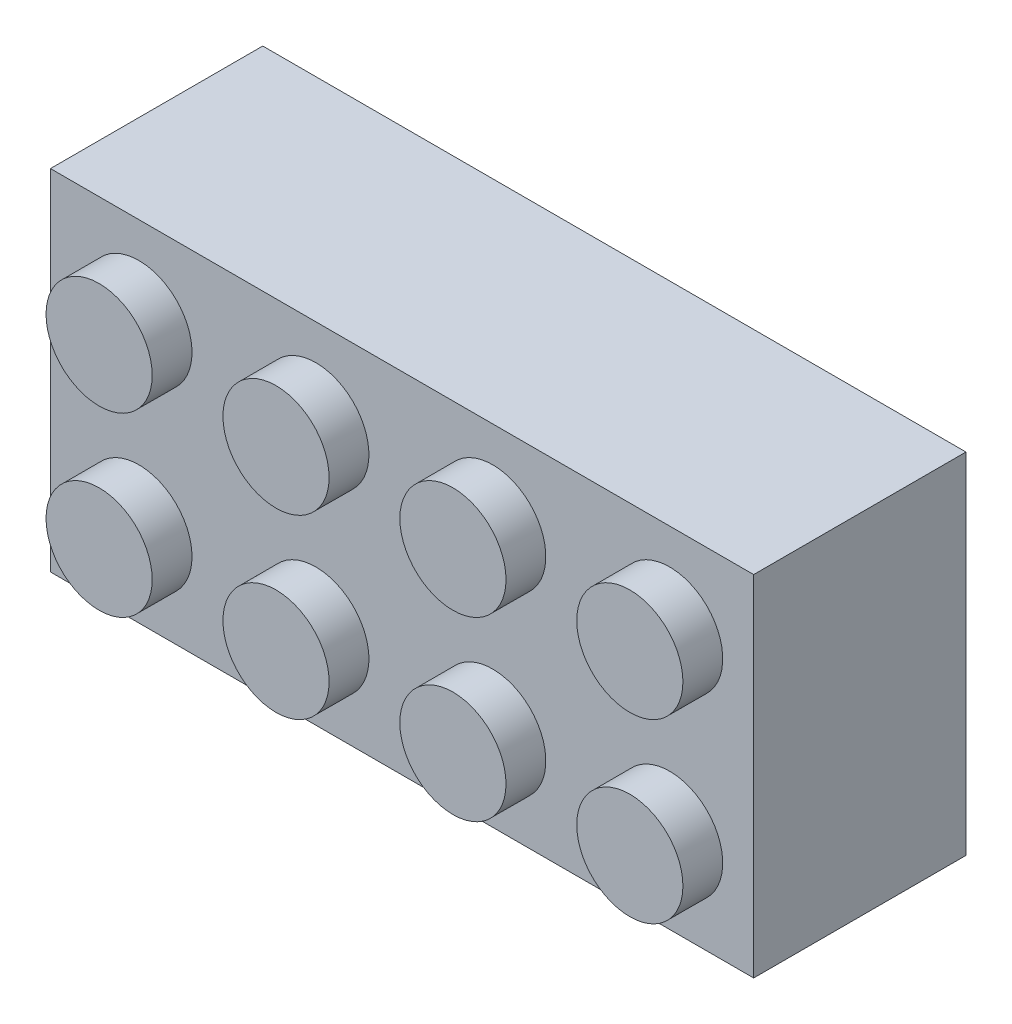
SolidWorks part; units mm, degrees
material "ABS"
ref_plane "Front Plane" through (0, 0, 0) normal (0, 0, 1) x (1, 0, 0)
ref_plane "Top Plane" through (0, 0, 0) normal (0, 1, 0) x (1, 0, 0)
ref_plane "Right Plane" through (0, 0, 0) normal (1, 0, 0) x (0, 0, -1)
sketch "Sketch1" plane through (0, 0, 0) normal (0, 0, 1) x (1, 0, 0)
  line L1 (-15.9, -7.9) -> (15.9, -7.9)
  line L2 (-15.9, -7.9) -> (-15.9, 7.9)
  line L3 (-15.9, 7.9) -> (15.9, 7.9)
  line L4 (15.9, -7.9) -> (15.9, 7.9)
  line L5 (-15.9, -7.9) -> (15.9, 7.9) construction
  line L6 (-15.9, 7.9) -> (15.9, -7.9) construction
  point P0 (0, 0)
  dimension "D1" = 31.8
  dimension "D2" = 15.8
extrude "Boss-Extrude1" add sketch "Sketch1" along normal blind 9.6
ref_plane "Plane1" through (0, 0, 9.6) normal (0, 0, 1) x (1, 0, 0)
sketch "Sketch2" plane through (0, 0, 9.6) normal (0, 0, 1) x (1, 0, 0)
  line L0 (-15.9, 7.9) -> (-15.9, -7.9) construction
  line L1 (15.9, 7.9) -> (-15.9, 7.9) construction
  circle A0 centre (-11.9, 3.9) radius 2.4
  circle A1 centre (-3.9, 3.9) radius 2.4
  circle A2 centre (4.1, 3.9) radius 2.4
  circle A3 centre (12.1, 3.9) radius 2.4
  circle A4 centre (-3.9, -4.1) radius 2.4
  circle A5 centre (4.1, -4.1) radius 2.4
  circle A6 centre (12.1, -4.1) radius 2.4
  circle A7 centre (-11.9, -4.1) radius 2.4
  dimension "D1" = 4.8
  dimension "D2" = 4
  dimension "D3" = 4
  dimension "D4" = 4
  dimension "D5" = 2
extrude "Boss-Extrude2" add sketch "Sketch2" along normal blind 1.8
sketch "Sketch3" plane through (0, 0, 9.6) normal (0, 0, 1) x (1, 0, 0)
  line L0 (-15.9, 7.9) -> (-15.9, -7.9) construction
  circle A0 centre (-11.9, 3.9) radius 1.3
  circle A2 centre (-3.9, 3.9) radius 1.3
  circle A3 centre (4.1, 3.9) radius 1.3
  circle A4 centre (12.1, 3.9) radius 1.3
  circle A5 centre (-3.9, -4.1) radius 1.3
  circle A6 centre (4.1, -4.1) radius 1.3
  circle A7 centre (12.1, -4.1) radius 1.3
  circle A8 centre (-11.9, -4.1) radius 1.3
  dimension "D1" = 2.6
  dimension "D2" = 4
  dimension "D3" = 4
  dimension "D4" = 2
extrude "Cut-Extrude1" cut sketch "Sketch3" against normal blind 20.7 from offset 0.7
sketch "Sketch4" plane through (0, 0, 0) normal (0, 0, 1) x (1, 0, 0)
  line L0 (0, 20.8206) -> (0, -20.114) construction
  line L1 (-15.9, 7.9) -> (-15.9, -7.9) construction
  line L2 (0, 0) -> (-22.9786, 0) construction
  line L3 (-14.7, 3.4) -> (-14.7, -3.4)
  line L4 (-14.7, -3.4) -> (-14.5, -3.4)
  line L5 (-14.5, -3.4) -> (-14.5, -4.6)
  line L6 (-14.5, -4.6) -> (-14.7, -4.6)
  line L7 (-14.7, -4.6) -> (-14.7, -6.7)
  line L8 (-14.7, -6.7) -> (-12.6, -6.7)
  line L9 (-12.6, -6.7) -> (-12.6, -6.5)
  line L10 (-12.6, -6.5) -> (-11.4, -6.5)
  line L11 (-11.4, -6.5) -> (-11.4, -6.7)
  line L12 (-11.4, -6.7) -> (-4.6, -6.7)
  line L13 (-4.6, -6.7) -> (-4.6, -6.5)
  line L14 (-4.6, -6.5) -> (-3.4, -6.5)
  line L15 (-3.4, -6.5) -> (-3.4, -6.7)
  line L16 (-3.4, -6.7) -> (-0.55, -6.7)
  line L17 (-15.9, -7.9) -> (15.9, -7.9) construction
  line L18 (-0.55, -6.7) -> (-0.55, -3.2031)
  line L19 (-3.25, 0) -> (-4.75, 0)
  line L20 (-11.25, 0) -> (-14.7, 0)
  line L21 (-0.55, 6.7) -> (-0.55, 3.2031)
  line L22 (-3.4, 6.7) -> (-0.55, 6.7)
  line L23 (-3.4, 6.5) -> (-3.4, 6.7)
  line L24 (-4.6, 6.5) -> (-3.4, 6.5)
  line L25 (-4.6, 6.7) -> (-4.6, 6.5)
  line L26 (-11.4, 6.7) -> (-4.6, 6.7)
  line L27 (-11.4, 6.5) -> (-11.4, 6.7)
  line L28 (-12.6, 6.5) -> (-11.4, 6.5)
  line L29 (-12.6, 6.7) -> (-12.6, 6.5)
  line L30 (-14.7, 6.7) -> (-12.6, 6.7)
  line L31 (-14.7, 4.6) -> (-14.7, 6.7)
  line L32 (-14.5, 4.6) -> (-14.7, 4.6)
  line L33 (-14.5, 3.4) -> (-14.5, 4.6)
  line L34 (-14.7, 3.4) -> (-14.5, 3.4)
  line L35 (0.55, -6.7) -> (0.55, -3.2031)
  line L36 (3.4, -6.7) -> (0.55, -6.7)
  line L37 (3.4, -6.5) -> (3.4, -6.7)
  line L38 (4.6, -6.5) -> (3.4, -6.5)
  line L39 (4.6, -6.7) -> (4.6, -6.5)
  line L40 (11.4, -6.7) -> (4.6, -6.7)
  line L41 (11.4, -6.5) -> (11.4, -6.7)
  line L42 (12.6, -6.5) -> (11.4, -6.5)
  line L43 (12.6, -6.7) -> (12.6, -6.5)
  line L44 (14.7, -6.7) -> (12.6, -6.7)
  line L45 (14.7, -4.6) -> (14.7, -6.7)
  line L46 (14.5, -4.6) -> (14.7, -4.6)
  line L47 (14.5, -3.4) -> (14.5, -4.6)
  line L48 (14.7, -3.4) -> (14.5, -3.4)
  line L49 (14.7, 3.4) -> (14.7, -3.4)
  line L50 (14.7, 3.4) -> (14.5, 3.4)
  line L51 (14.5, 3.4) -> (14.5, 4.6)
  line L52 (14.5, 4.6) -> (14.7, 4.6)
  line L53 (14.7, 4.6) -> (14.7, 6.7)
  line L54 (14.7, 6.7) -> (12.6, 6.7)
  line L55 (12.6, 6.7) -> (12.6, 6.5)
  line L56 (12.6, 6.5) -> (11.4, 6.5)
  line L57 (11.4, 6.5) -> (11.4, 6.7)
  line L58 (11.4, 6.7) -> (4.6, 6.7)
  line L59 (4.6, 6.7) -> (4.6, 6.5)
  line L60 (4.6, 6.5) -> (3.4, 6.5)
  line L61 (3.4, 6.5) -> (3.4, 6.7)
  line L62 (3.4, 6.7) -> (0.55, 6.7)
  line L63 (0.55, 6.7) -> (0.55, 3.2031)
  circle A0 centre (0, 0) radius 3.25
  circle A1 centre (8, 0) radius 3.25
  circle A2 centre (-8, 0) radius 3.25
  circle A3 centre (8, 0) radius 2.05
  circle A4 centre (0, 0) radius 2.05
  circle A5 centre (-8, 0) radius 2.05
  arc A6 (-0.55, -3.2031) -> (-0.55, 3.2031) centre (0, 0) cw
  circle A7 centre (-8, 0) radius 3.25
  arc A8 (0.55, -3.2031) -> (0.55, 3.2031) centre (0, 0) ccw
  point P20 (-14.5, -4)
  point P32 (-12, -6.5)
  point P33 (-4, -6.5)
  dimension "D1" = 2
  dimension "D2" = 6.5
  dimension "D4" = 4
  dimension "D5" = 4
  dimension "D6" = 4
  dimension "D7" = 1.2
  dimension "D8" = 1.2
  dimension "D9" = 1.2
  dimension "D10" = 0.2
  dimension "D11" = 0.55
  dimension "D3" = 1.2
extrude "Cut-Extrude3" cut sketch "Sketch4" along normal blind 8.6 contours A1 A3 | L19 A2 L20 L3 L4 L5 L6 L7 L8 L9 L10 L11 L12 L13 L14 L15 L16 L18 A0 | L20 A2 L19 A0 L21 L22 L23 L24 L25 L26 L27 L28 L29 L30 L31 L32 L33 L34 L3 | A5 | A3 | A4 | L35 A8 L63 L62 L61 L60 L59 L58 L57 L56 L55 L54 L53 L52 L51 L50 L49 L48 L47 L46 L45 L44 L43 L42 L41 L40 L39 L38 L37 L36
sketch "Sketch5" plane through (0, 0, 0) normal (0, 0, 1) x (1, 0, 0)
  line L0 (0.55, 6.7) -> (-0.55, 6.7)
  line L1 (0.55, 6.7) -> (0.55, 3.2031) construction
  line L2 (3.4, 6.7) -> (0.55, 6.7) construction
  line L3 (-0.55, 6.7) -> (-0.55, 3.2031)
  line L4 (0.55, 6.7) -> (0.55, 3.2031)
  line L5 (6.27, 0) -> (-6.27, 0) construction
  line L6 (0.55, -6.7) -> (-0.55, -6.7)
  line L7 (-0.55, -6.7) -> (-0.55, -3.2031)
  line L8 (0.55, -6.7) -> (0.55, -3.2031)
  arc A0 (0.55, 3.2031) -> (-0.55, 3.2031) centre (0, 0) ccw
  arc A1 (-0.55, 3.2031) -> (-0.55, -3.2031) centre (0, 0) ccw construction
  arc A2 (0.55, -3.2031) -> (-0.55, -3.2031) centre (0, 0) cw
extrude "Cut-Extrude4" cut sketch "Sketch5" along normal blind 2.3
